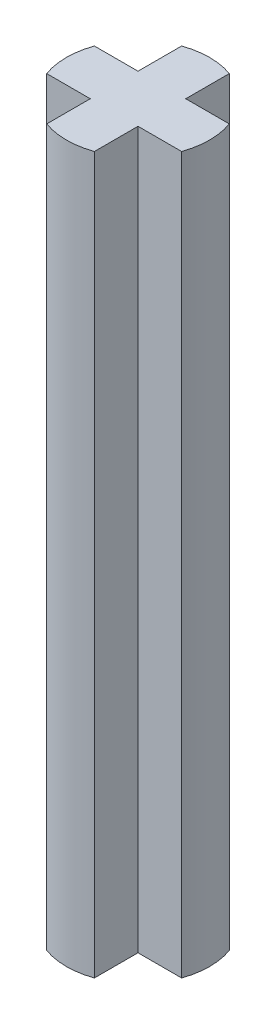
SolidWorks part; units mm, degrees
ref_plane "Front Plane" through (0, 0, 0) normal (0, 0, 1) x (1, 0, 0)
ref_plane "Top Plane" through (0, 0, 0) normal (0, 1, 0) x (1, 0, 0)
ref_plane "Right Plane" through (0, 0, 0) normal (1, 0, 0) x (0, 0, -1)
sketch "Sketch1" plane through (0, 0, 0) normal (0, 1, 0) x (1, 0, 0)
  line L1 (-1.5, -0.5) -> (1.5, -0.5)
  line L2 (-1.5, -0.5) -> (-1.5, 0.5)
  line L3 (-1.5, 0.5) -> (1.5, 0.5)
  line L4 (1.5, -0.5) -> (1.5, 0.5)
  line L5 (-1.5, -0.5) -> (1.5, 0.5) construction
  line L6 (-1.5, 0.5) -> (1.5, -0.5) construction
  line L7 (-0.5, -1.5) -> (0.5, -1.5)
  line L8 (-0.5, -1.5) -> (-0.5, 1.5)
  line L9 (-0.5, 1.5) -> (0.5, 1.5)
  line L10 (0.5, -1.5) -> (0.5, 1.5)
  line L11 (-0.5, -1.5) -> (0.5, 1.5) construction
  line L12 (-0.5, 1.5) -> (0.5, -1.5) construction
  point P0 (0, 0)
  point P6 (0, 0)
  dimension "D1" = 1
  dimension "D2" = 3
extrude "Boss-Extrude1" add sketch "Sketch1" along normal blind 15 contours L4 L3 L2 L1 | L10 L9 L8 L7
sketch "Sketch2" plane through (0, 15, 0) normal (0, 1, 0) x (1, 0, 0)
  circle A0 centre (0, 0) radius 1.5
extrude "Cut-Extrude1" cut sketch "Sketch2" against normal up to next (15 mm away) flip side to cut contours A0
